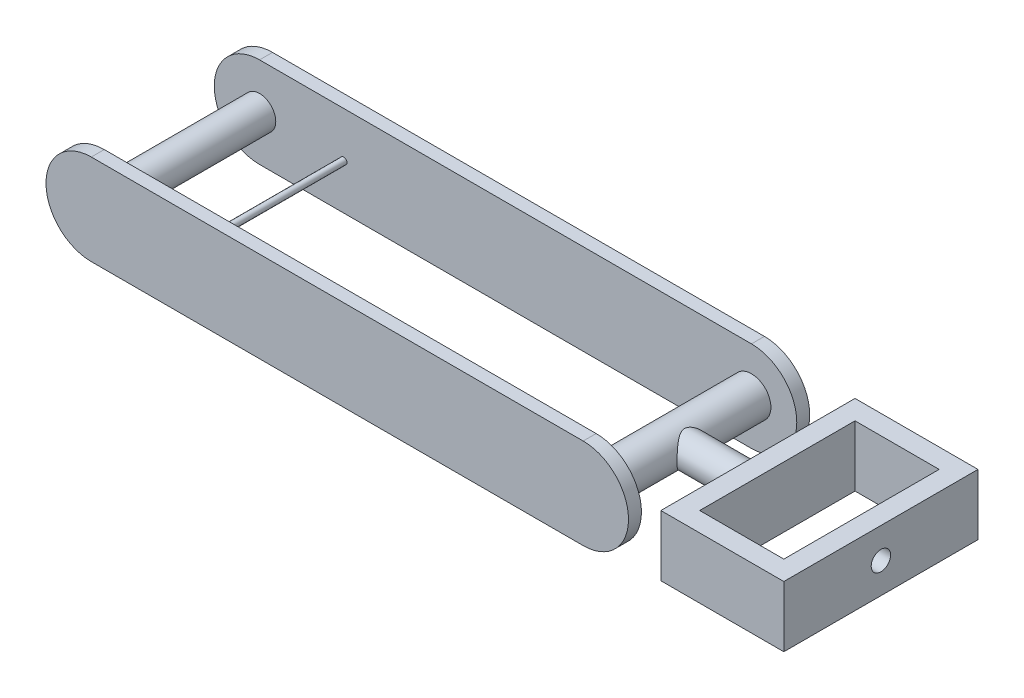
SolidWorks part; units mm, degrees
ref_plane "Front Plane" through (0, 0, 0) normal (0, 0, 1) x (1, 0, 0)
ref_plane "Top Plane" through (0, 0, 0) normal (0, 1, 0) x (1, 0, 0)
ref_plane "Right Plane" through (0, 0, 0) normal (1, 0, 0) x (0, 0, -1)
sketch "Sketch1" plane through (0, 0, 0) normal (0, 0, 1) x (1, 0, 0)
  line L0 (-190, 0) -> (190, 0) construction
  line L1 (-190, 35) -> (190, 35)
  line L2 (-190, -35) -> (190, -35)
  arc A0 (-190, 35) -> (-190, -35) centre (-190, 0) ccw
  arc A1 (190, -35) -> (190, 35) centre (190, 0) ccw
  point P2 (0, 0)
  point P8 (225, 0)
  point P9 (-225, 0)
  dimension "D1" = 450
  dimension "D2" = 70
extrude "Boss-Extrude1" add sketch "Sketch1" along normal blind 10
ref_plane "Plane1" through (0, 0, -120) normal (0, 0, 1) x (1, 0, 0)
sketch "Sketch2" plane through (0, 0, -120) normal (0, 0, 1) x (1, 0, 0)
  line L0 (-190, 0) -> (190, 0) construction
  line L1 (-190, 35) -> (190, 35)
  line L2 (-190, -35) -> (190, -35)
  arc A0 (-190, 35) -> (-190, -35) centre (-190, 0) ccw
  arc A1 (190, -35) -> (190, 35) centre (190, 0) ccw
  point P2 (0, 0)
  point P8 (225, 0)
  point P9 (-225, 0)
  dimension "D1" = 450
  dimension "D2" = 70
extrude "Boss-Extrude2" add sketch "Sketch2" against normal blind 10 separate body
sketch "Sketch3" plane through (0, 0, 10) normal (0, 0, 1) x (1, 0, 0)
  line L0 (-225, 0) -> (225, 0) construction
  arc A0 (-190, 35) -> (-190, -35) centre (-190, 0) ccw construction
  arc A1 (190, -35) -> (190, 35) centre (190, 0) ccw construction
  circle A2 centre (-190, 0) radius 12.5
  dimension "D1" = 25
extrude "Boss-Extrude3" add sketch "Sketch3" against normal blind 145
sketch "Sketch4" plane through (0, 0, 10) normal (0, 0, 1) x (1, 0, 0)
  line L0 (0, 0) -> (-225, 0) construction
  arc A0 (-190, 35) -> (-190, -35) centre (-190, 0) ccw construction
  circle A1 centre (-125, 0) radius 2.5
  point P6 (-125, 0)
  dimension "D2" = 5
  dimension "D1" = 100
extrude "Boss-Extrude4" add sketch "Sketch4" against normal blind 145
sketch "Sketch5" plane through (0, 0, 10) normal (0, 0, 1) x (1, 0, 0)
  circle A0 centre (190, 0) radius 15
  dimension "D1" = 30
extrude "Boss-Extrude5" add sketch "Sketch5" against normal blind 145
ref_plane "Plane2" through (190, 0, 0) normal (1, 0, 0) x (0, 0, -1)
sketch "Sketch6" plane through (190, 0, 0) normal (1, 0, 0) x (0, 0, -1)
  line L0 (0, 0) -> (120, 0) construction
  line L1 (120, 15) -> (120, -15) construction
  circle A0 centre (60, 0) radius 12.5
  point P5 (60, 0)
  dimension "D1" = 25
extrude "Boss-Extrude6" add sketch "Sketch6" along normal blind 65
sketch "Sketch7" plane through (255, 0, 0) normal (1, 0, 0) x (0, 0, -1)
  line L0 (60, 12.5) -> (60, -12.5) construction
  line L1 (72.5, 0) -> (47.5, 0) construction
  line L3 (-15, 23.5029) -> (135, 23.5029)
  line L4 (-15, 23.5029) -> (-15, -23.5029)
  line L5 (-15, -23.5029) -> (135, -23.5029)
  line L6 (135, 23.5029) -> (135, -23.5029)
  line L7 (-15, 23.5029) -> (135, -23.5029) construction
  line L8 (-15, -23.5029) -> (135, 23.5029) construction
  circle A0 centre (60, 0) radius 12.5 construction
  circle A1 centre (60, 0) radius 12.5 construction
  point P9 (60, 0)
  dimension "D1" = 150
extrude "Boss-Extrude7" add sketch "Sketch7" along normal blind 15
sketch "Sketch9" plane through (270, 0, 0) normal (1, 0, 0) x (0, 0, -1)
  line L0 (-15, 0) -> (135, 0) construction
  line L1 (-15, 23.5029) -> (-15, -23.5029) construction
  line L2 (135, -23.5029) -> (135, 23.5029) construction
  line L3 (60, 23.5029) -> (60, -23.5029) construction
  line L4 (135, 23.5029) -> (-15, 23.5029) construction
  line L5 (-15, -23.5029) -> (135, -23.5029) construction
  line L6 (120.1649, 23.5029) -> (120, -23.5029) construction
  line L7 (120, 35) -> (120, -35) construction
  line L8 (0, 23.5029) -> (0, -23.5029) construction
  line L10 (-15, 23.5029) -> (0, 23.5029)
  line L11 (-15, 23.5029) -> (-15, -23.5029)
  line L12 (-15, -23.5029) -> (0, -23.5029)
  line L13 (0, 23.5029) -> (0, -23.5029)
  line L14 (135, 23.5029) -> (120, 23.5029)
  line L15 (135, 23.5029) -> (135, -23.5029)
  line L16 (135, -23.5029) -> (120, -23.5029)
  line L17 (120, 23.5029) -> (120, -23.5029)
extrude "Boss-Extrude8" add sketch "Sketch9" along normal blind 65
sketch "Sketch10" plane through (335, 0, 0) normal (1, 0, 0) x (0, 0, -1)
  line L1 (-15, 23.5029) -> (135, 23.5029)
  line L2 (-15, 23.5029) -> (-15, -23.5029)
  line L3 (-15, -23.5029) -> (135, -23.5029)
  line L4 (135, 23.5029) -> (135, -23.5029)
extrude "Boss-Extrude9" add sketch "Sketch10" along normal blind 15
sketch "Sketch11" plane through (350, 0, 0) normal (1, 0, 0) x (0, 0, -1)
  line L0 (-15, 0) -> (135, 0) construction
  line L2 (-15, 23.5029) -> (-15, -23.5029) construction
  line L3 (135, -23.5029) -> (135, 23.5029) construction
  circle A0 centre (60, 0) radius 7.5
  dimension "D1" = 15
extrude "Cut-Extrude1" cut sketch "Sketch11" against normal blind 15
